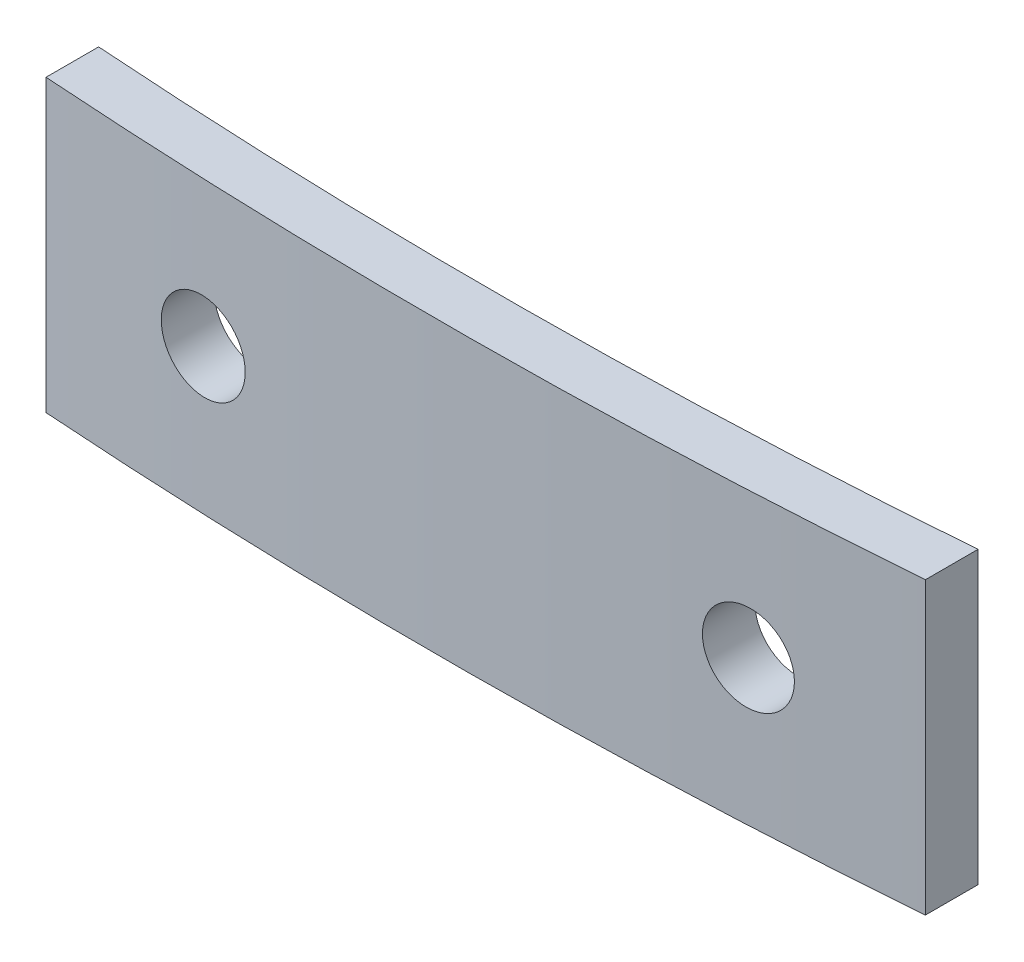
SolidWorks part; units mm, degrees
ref_plane "Front Plane" through (0, 0, 0) normal (0, 0, 1) x (1, 0, 0)
ref_plane "Top Plane" through (0, 0, 0) normal (0, 1, 0) x (1, 0, 0)
ref_plane "Right Plane" through (0, 0, 0) normal (1, 0, 0) x (0, 0, -1)
sketch "Sketch1" plane through (0, 0, 0) normal (0, 1, 0) x (1, 0, 0)
  line L0 (-35, 4.1426) -> (35, 4.5206) construction
  line L4 (-17.5, 10.9426) -> (-17.5, -8.9719) construction
  line L7 (-22.5, 18.3807) -> (-22.5, -8.9719) construction
  line L8 (22.5, 18.3807) -> (22.5, -9.9995) construction
  line L9 (17.5, -9.9995) -> (17.5, 10.9426) construction
  line L13 (-12.5, -8.9719) -> (-12.5, 10.9426) construction
  line L14 (12.5, 10.9426) -> (12.5, -9.9995) construction
  line L15 (-12.5, -2.2948) -> (-12.5, -3.7984)
  line L16 (12.5, -2.1651) -> (12.5, -3.6699)
  arc A5 (-12.5, -2.2948) -> (12.5, -2.1651) centre (-0.865, 164.5106) ccw
  arc A6 (-12.5, -3.7984) -> (12.5, -3.6699) centre (-0.865, 164.5106) ccw
  arc A8 (-35.4132, 0.908) -> (35.4342, 1.2875) centre (-0.865, 164.5106) ccw construction
  arc A9 (-35.7232, -0.5597) -> (35.7598, -0.1767) centre (-0.865, 164.5106) ccw construction
  point P4 (-35, 4.1426)
  point P5 (-35, 2.8648)
  point P7 (38.108, 5.4708)
  point P8 (35, 4.5206)
  point P10 (-0.865, 164.5106)
  point P11 (35, 3.2398)
  point P18 (-31.892, 5.0928)
  dimension "D1" = 45
  dimension "D2" = 1.5
  dimension "D3" = 70
  dimension "D4" = 22.5
  dimension "D6" = 17.5
  dimension "D5" = 35
  dimension "D7" = 25
  dimension "D8" = 12.5
extrude "Boss-Extrude1" add sketch "Sketch1" along normal blind 8.3
sketch "Sketch2" plane through (0, 0, 0) normal (0, 0, 1) x (1, 0, 0)
  line L0 (0, 8.3) -> (0, 0) construction
  line L1 (12.5, 8.3) -> (-12.5, 8.3) construction
  line L2 (-9, 4.15) -> (-6.5, 4.15) construction
  line L5 (6.5, 4.15) -> (9, 4.15) construction
  circle A0 centre (-7.75, 4.15) radius 1.25
  circle A1 centre (7.75, 4.15) radius 1.25
  point P15 (0, 0)
  dimension "D2" = 2.5
  dimension "D3" = 2.5
  dimension "D1" = 15.5
  dimension "D4" = 7.75
extrude "Cut-Extrude1" cut sketch "Sketch2" against normal through all both and the other way through all
